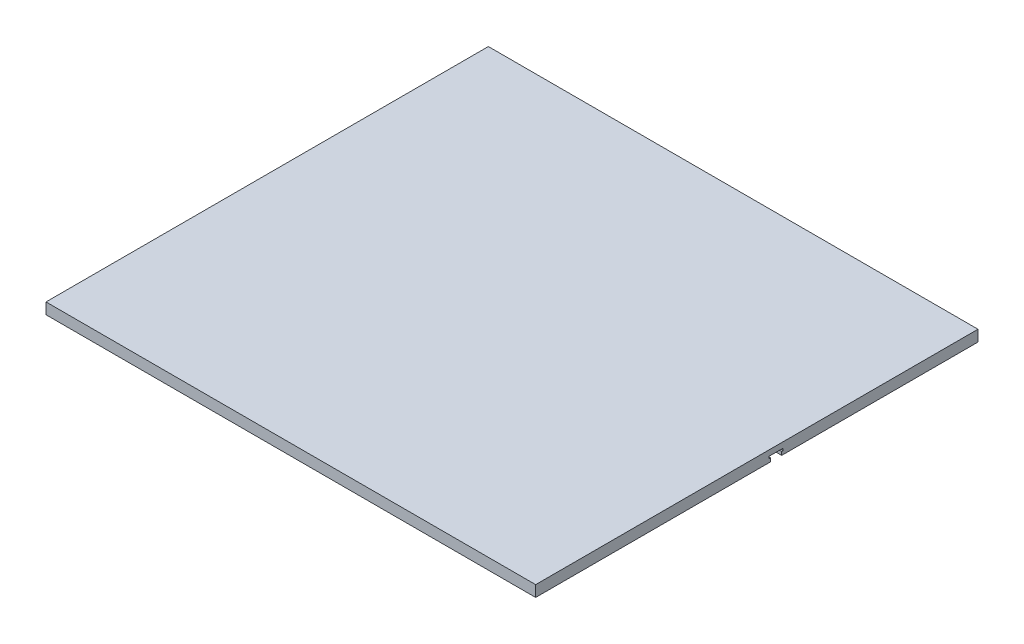
SolidWorks part; units mm, degrees
material "Oak"
ref_plane "Front Plane" through (0, 0, 0) normal (0, 0, 1) x (1, 0, 0)
ref_plane "Top Plane" through (0, 0, 0) normal (0, 1, 0) x (1, 0, 0)
ref_plane "Right Plane" through (0, 0, 0) normal (1, 0, 0) x (0, 0, -1)
sketch "Sketch1" plane through (0, 0, 0) normal (0, 1, 0) x (1, 0, 0)
  line L1 (0, 0) -> (838.2, 0)
  line L2 (0, 0) -> (0, 757.2375)
  line L3 (0, 757.2375) -> (838.2, 757.2375)
  line L4 (838.2, 0) -> (838.2, 757.2375)
  dimension "D1" = 757.2375
  dimension "D2" = 838.2
extrude "Boss-Extrude1" add sketch "Sketch1" along normal blind 19.05
chamfer "Chamfer1" [suppressed] distance 2.54 angle 45
sketch "Sketch2" plane through (838.2, 0, 0) normal (1, 0, 0) x (0, 0, -1)
  circle A0 centre (415.3281, 124.6124) radius 433.6193 construction
  dimension "D1" = 867.2386
  dimension "D2" = 341.9094
sketch "Sketch3" plane through (838.2, 0, 0) normal (1, 0, 0) x (0, 0, -1)
  line L0 (421.1765, 0) -> (421.1765, 5.9627)
  line L3 (423.8435, 5.9627) -> (423.8435, 9.5187)
  line L5 (399.4595, 9.5187) -> (399.4595, 5.9627)
  line L8 (402.1265, 5.9627) -> (402.1265, 0)
  line L13 (399.4595, 5.9627) -> (402.1265, 5.9627)
  line L15 (402.1265, 0) -> (421.1765, 0)
  line L17 (421.1765, 5.9627) -> (423.8435, 5.9627)
  line L21 (424.3515, 10.5347) -> (398.9515, 10.5347) construction
  line L22 (398.9515, 10.5347) -> (398.9515, 5.9627) construction
  line L23 (424.3515, 5.9627) -> (424.3515, 10.5347) construction
  line L24 (423.8435, 9.5187) -> (399.4595, 9.5187)
  line L25 (423.8435, 10.0267) -> (399.4595, 10.0267) construction
  line L26 (399.4595, 6.4707) -> (402.1265, 6.4707) construction
  line L27 (421.1765, 6.4707) -> (423.8435, 6.4707) construction
  line L28 (401.6185, 5.9627) -> (401.6185, 0) construction
  line L29 (421.6845, 0) -> (421.6845, 5.9627) construction
  line L30 (402.1265, 6.4707) -> (402.1265, 0.508) construction
  line L31 (401.6185, 0) -> (421.6845, 0) construction
  line L32 (421.1765, 0.508) -> (421.1765, 6.4707) construction
  line L33 (402.1265, 0.508) -> (421.1765, 0.508) construction
  line L34 (398.9515, 5.9627) -> (401.6185, 5.9627) construction
  line L35 (399.4595, 10.0267) -> (399.4595, 6.4707) construction
  line L36 (423.8435, 6.4707) -> (423.8435, 10.0267) construction
  line L37 (421.6845, 5.9627) -> (424.3515, 5.9627) construction
  line L38 (411.6515, 9.5187) -> (411.6515, 0) construction
  line L39 (0, 0) -> (757.2375, 0) construction
  point P16 (423.8435, 7.7407)
  dimension "D1" = 399.4595
  dimension "D3" = 19.05
  dimension "D4" = 5.9627
  dimension "D2" = 24.384
  dimension "D5" = 9.5187
extrude "Cut-Extrude1" cut sketch "Sketch3" against normal through all
